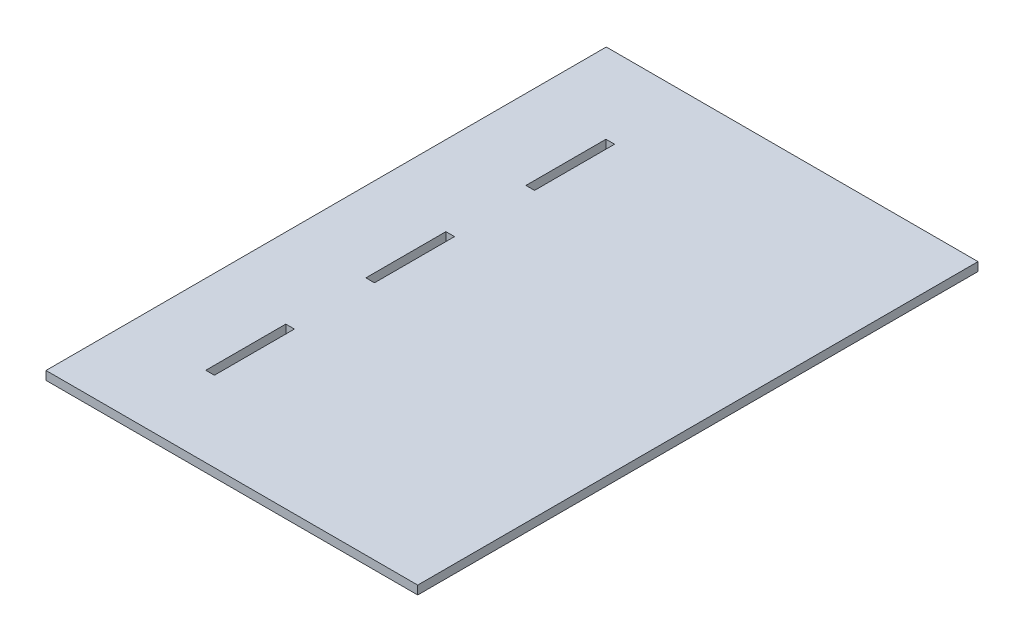
SolidWorks part; units mm, degrees
material "A-Glass Fiber"
ref_plane "Front Plane" through (0, 0, 0) normal (0, 0, 1) x (1, 0, 0)
ref_plane "Top Plane" through (0, 0, 0) normal (0, 1, 0) x (1, 0, 0)
ref_plane "Right Plane" through (0, 0, 0) normal (1, 0, 0) x (0, 0, -1)
sketch "Sketch1" plane through (0, 0, 0) normal (0, 1, 0) x (1, 0, 0)
  line L0 (427.99, -558.8) -> (427.99, -467.36) construction
  line L1 (0, 0) -> (438.15, 0)
  line L2 (0, 0) -> (0, -660.4)
  line L3 (0, -660.4) -> (438.15, -660.4)
  line L4 (438.15, 0) -> (438.15, -660.4)
  line L7 (93.98, 0) -> (104.14, 0)
  line L8 (93.98, 0) -> (93.98, -94.3429)
  line L9 (93.98, -94.3429) -> (104.14, -94.3429)
  line L10 (104.14, 0) -> (104.14, -94.3429)
  line L11 (104.14, -94.3429) -> (93.98, -94.3429)
  line L12 (104.14, -94.3429) -> (104.14, -188.6857)
  line L13 (104.14, -188.6857) -> (93.98, -188.6857)
  line L14 (93.98, -94.3429) -> (93.98, -188.6857)
  line L15 (93.98, -188.6857) -> (104.14, -188.6857)
  line L16 (93.98, -188.6857) -> (93.98, -283.0286)
  line L17 (93.98, -283.0286) -> (104.14, -283.0286)
  line L18 (104.14, -188.6857) -> (104.14, -283.0286)
  line L19 (104.14, -283.0286) -> (93.98, -283.0286)
  line L20 (104.14, -283.0286) -> (104.14, -377.3714)
  line L21 (104.14, -377.3714) -> (93.98, -377.3714)
  line L22 (93.98, -283.0286) -> (93.98, -377.3714)
  line L23 (93.98, -377.3714) -> (104.14, -377.3714)
  line L24 (93.98, -377.3714) -> (93.98, -471.7143)
  line L25 (93.98, -471.7143) -> (104.14, -471.7143)
  line L26 (104.14, -377.3714) -> (104.14, -471.7143)
  line L27 (104.14, -471.7143) -> (93.98, -471.7143)
  line L28 (104.14, -471.7143) -> (104.14, -566.0571)
  line L29 (104.14, -566.0571) -> (93.98, -566.0571)
  line L30 (93.98, -471.7143) -> (93.98, -566.0571)
  line L31 (93.98, -566.0571) -> (104.14, -566.0571)
  line L32 (93.98, -566.0571) -> (93.98, -660.4)
  line L33 (93.98, -660.4) -> (104.14, -660.4)
  line L34 (104.14, -566.0571) -> (104.14, -660.4)
  dimension "D1" = 438.15
  dimension "D2" = 660.4
  dimension "D3" = 323.85
  dimension "D4" = 10.16
extrude "Boss-Extrude1" add sketch "Sketch1" along normal blind 10.16 contours L32 L30 L24 L22 L16 L14 L8 L1 L2 L3 | L28 L34 L3 L4 L1 L10 L12 L18 L20 L26 | L10 L1 L8 L9 | L18 L13 L16 L17 | L26 L21 L24 L25 | L34 L29 L32 L3
